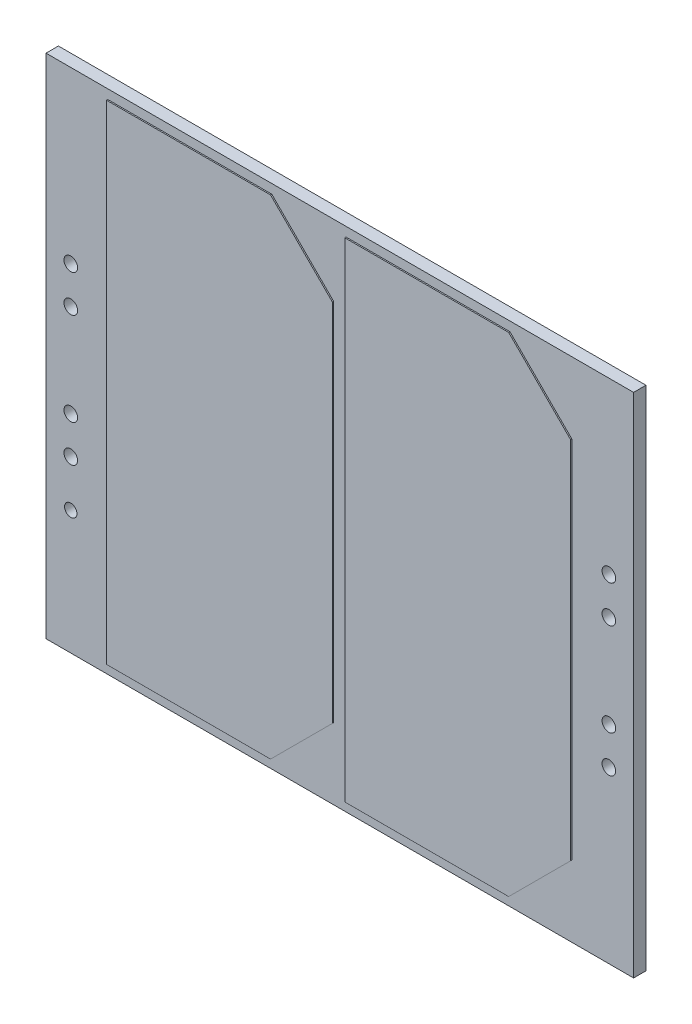
SolidWorks part; units mm, degrees
ref_plane "Front Plane" through (0, 0, 0) normal (0, 0, 1) x (1, 0, 0)
ref_plane "Top Plane" through (0, 0, 0) normal (0, 1, 0) x (1, 0, 0)
ref_plane "Right Plane" through (0, 0, 0) normal (1, 0, 0) x (0, 0, -1)
sketch "Sketch1" plane through (0, 0, 0) normal (0, 0, 1) x (1, 0, 0)
  line L0 (-43.5, 41) -> (-43.5, -41) construction
  line L1 (-47.5, -41) -> (47.5, -41)
  line L2 (-47.5, -41) -> (-47.5, 41)
  line L3 (-47.5, 41) -> (47.5, 41)
  line L4 (47.5, -41) -> (47.5, 41)
  line L5 (-47.5, -41) -> (47.5, 41) construction
  line L6 (-47.5, 41) -> (47.5, -41) construction
  line L7 (43.5, 41) -> (43.5, -41) construction
  circle A0 centre (-43.5, 13.5) radius 1.1
  circle A1 centre (-43.5, -13.5) radius 1.1
  circle A3 centre (43.5, 7.5) radius 1.1
  circle A4 centre (43.5, -7.5) radius 1.1
  circle A5 centre (-43.5, 7.5) radius 1.1
  circle A6 centre (-43.5, -7.5) radius 1.1
  circle A7 centre (43.5, 13.5) radius 1.1
  circle A8 centre (43.5, -13.5) radius 1.1
  circle A10 centre (-43.5, -21) radius 1
  point P0 (0, 0)
  dimension "D3" = 2.2
  dimension "D10" = 2.2
  dimension "D15" = 2
  dimension "D1" = 82
  dimension "D2" = 95
  dimension "D7" = 4
  dimension "D8" = 15
  dimension "D11" = 4
  dimension "D4" = 6
  dimension "D5" = 6
  dimension "D6" = 15
  dimension "D12" = 27.5
  dimension "D9" = 6
  dimension "D13" = 6
  dimension "D14" = 27.5
  dimension "D16" = 7.5
extrude "Boss-Extrude1" add sketch "Sketch1" along normal blind 2 contours A4 L7 A3 L3 L2 L1 A5 A1 A0
sketch "Sketch2" plane through (0, 0, 2) normal (0, 0, 1) x (1, 0, 0)
  line L0 (-11, 39.5) -> (-1, 29.5)
  line L1 (-37.5, 39.5) -> (-11, 39.5)
  line L2 (-37.5, 39.5) -> (-37.5, -39.5)
  line L3 (-37.5, -39.5) -> (-11, -39.5)
  line L4 (-1, 29.5) -> (-1, -29.5)
  line L5 (-37.5, 39.5) -> (-1, -39.5) construction
  line L6 (-37.5, -39.5) -> (-1, 39.5) construction
  line L43 (1, 39.5) -> (27.5, 39.5)
  line L44 (1, 39.5) -> (1, -39.5)
  line L45 (1, -39.5) -> (27.5, -39.5)
  line L46 (37.5, 29.5) -> (37.5, -29.5)
  line L47 (1, 39.5) -> (37.5, -39.5) construction
  line L48 (1, -39.5) -> (37.5, 39.5) construction
  line L49 (-1, -29.5) -> (-11, -39.5)
  line L62 (27.5, -39.5) -> (37.5, -29.5)
  line L63 (27.5, 39.5) -> (37.5, 29.5)
  line L64 (-47.5, -41) -> (-47.5, 41) construction
  line L65 (47.5, -41) -> (47.5, 41) construction
  point P4 (-19.25, 0)
  point P39 (19.25, 0)
  point P76 (47.5, 0)
  dimension "D25" = 10
  dimension "D26" = 10
  dimension "D3" = 2
extrude "Boss-Extrude2" add sketch "Sketch2" along normal blind 0.2
equation "\"D10@Sketch1\"=\"D3@Sketch1\""
equation "\"D5@Sketch1\"=\"D4@Sketch1\""
equation "\"D12@Sketch1\"=(\"D1@Sketch1\"-\"D6@Sketch1\"-\"D4@Sketch1\"*2)/2"
equation "\"D9@Sketch1\"=\"D4@Sketch1\""
equation "\"D13@Sketch1\"=\"D9@Sketch1\""
equation "\"D14@Sketch1\"=(\"D1@Sketch1\"-\"D8@Sketch1\"-\"D4@Sketch1\"*2)/2"
equation "\"D26@Sketch2\"=\"D25@Sketch2\""
